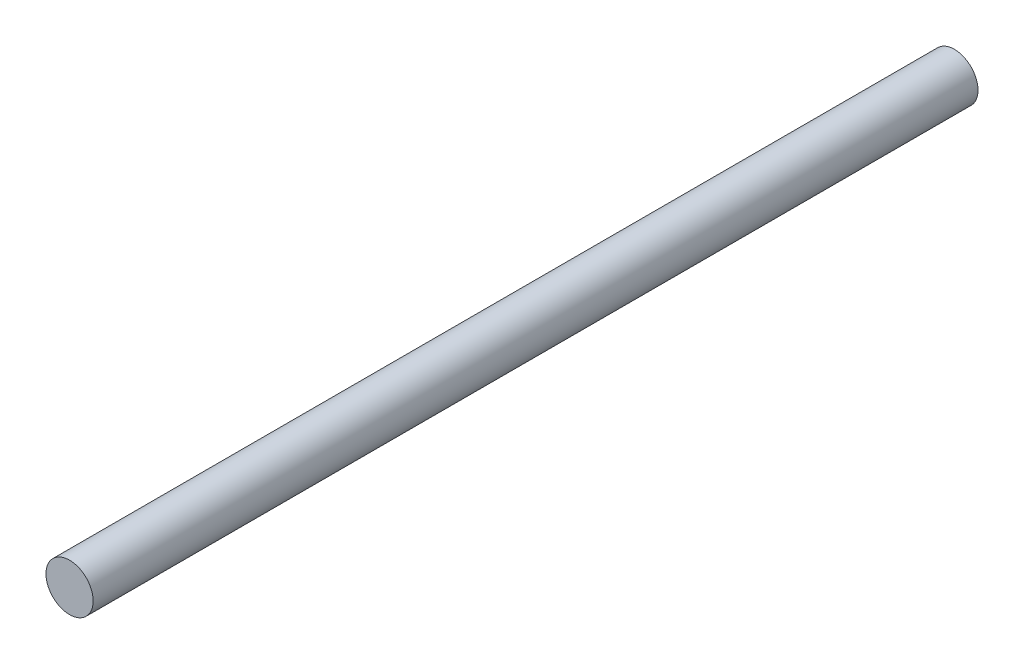
SolidWorks part; units mm, degrees
ref_plane "前视基准面" through (0, 0, 0) normal (0, 0, 1) x (1, 0, 0)
ref_plane "上视基准面" through (0, 0, 0) normal (0, 1, 0) x (1, 0, 0)
ref_plane "右视基准面" through (0, 0, 0) normal (1, 0, 0) x (0, 0, -1)
other "Configuration Table"
sketch "草图1" plane through (0, 0, 0) normal (0, 0, 1) x (1, 0, 0)
  circle A0 centre (0, 0) radius 2
  dimension "D1" = 4
extrude "凸台-拉伸1" add sketch "草图1" along normal blind 75
